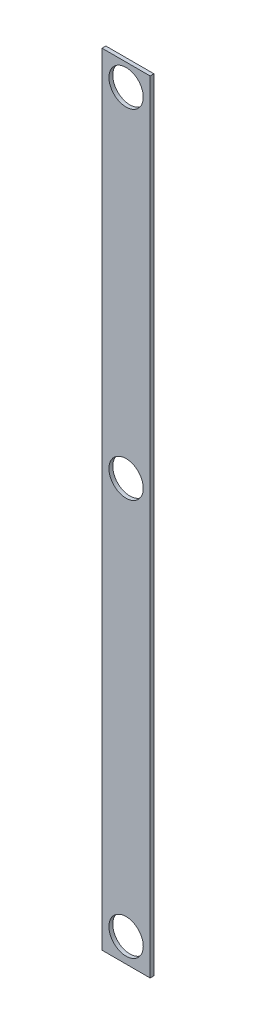
SolidWorks part; units mm, degrees
ref_plane "Front Plane" through (0, 0, 0) normal (0, 0, 1) x (1, 0, 0)
ref_plane "Top Plane" through (0, 0, 0) normal (0, 1, 0) x (1, 0, 0)
ref_plane "Right Plane" through (0, 0, 0) normal (1, 0, 0) x (0, 0, -1)
sketch "Sketch1" plane through (0, 0, 0) normal (0, 0, 1) x (1, 0, 0)
  line L1 (0, 0) -> (40, 0)
  line L2 (0, 0) -> (0, -650)
  line L3 (0, -650) -> (40, -650)
  line L4 (40, 0) -> (40, -650)
  dimension "D1" = 650
  dimension "D2" = 40
extrude "Boss-Extrude1" add sketch "Sketch1" along normal blind 3.175
sketch "Sketch2" plane through (0, 0, 3.175) normal (0, 0, 1) x (1, 0, 0)
  line L0 (40, 0) -> (0, 0) construction
  line L1 (20, 0) -> (20, -650) construction
  line L2 (0, -650) -> (40, -650) construction
  line L3 (0, -650) -> (40, -650) construction
  circle A0 centre (20, -18.1414) radius 14.279
  circle A1 centre (20, -630) radius 14.279
  circle A2 centre (20, -300) radius 14.279
  point P9 (20, -650)
  dimension "D1" = 28.558
  dimension "D2" = 28.558
  dimension "D4" = 28.558
  dimension "D5" = 300
  dimension "D3" = 20
extrude "Cut-Extrude1" cut sketch "Sketch2" against normal through all
